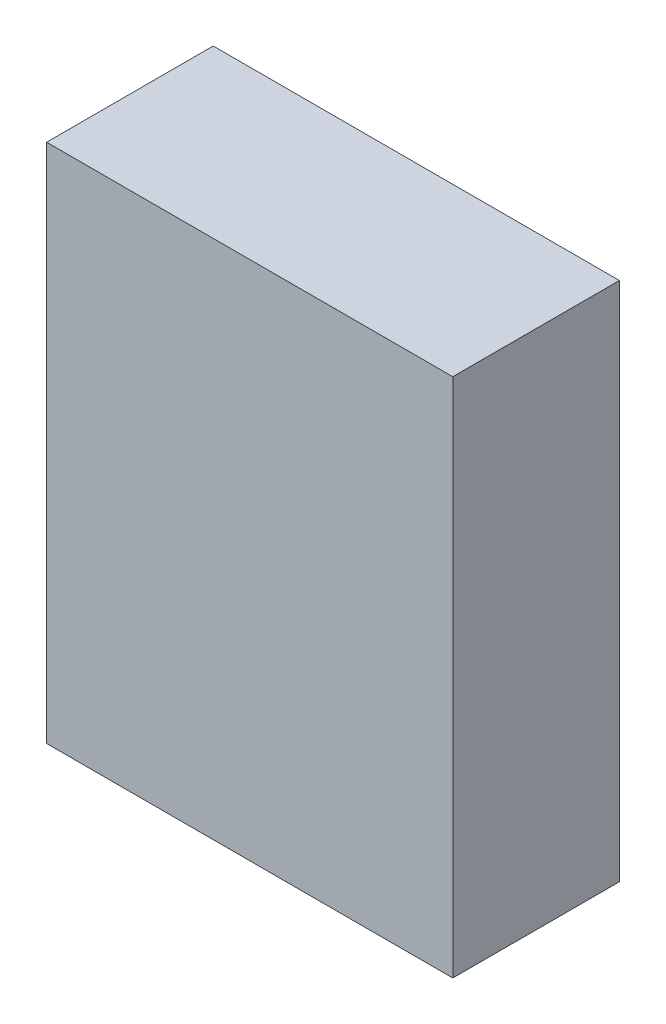
SolidWorks part; units mm, degrees
ref_plane "Front Plane" through (0, 0, 0) normal (0, 0, 1) x (1, 0, 0)
ref_plane "Top Plane" through (0, 0, 0) normal (0, 1, 0) x (1, 0, 0)
ref_plane "Right Plane" through (0, 0, 0) normal (1, 0, 0) x (0, 0, -1)
sketch "Sketch1" plane through (0, 0, 0) normal (0, 0, 1) x (1, 0, 0)
  line L1 (0, 0) -> (99.06, 0)
  line L2 (0, 0) -> (0, 127)
  line L3 (0, 127) -> (99.06, 127)
  line L4 (99.06, 0) -> (99.06, 127)
  dimension "D1" = 127
  dimension "D2" = 99.06
extrude "Boss-Extrude1" add sketch "Sketch1" along normal blind 40.64
